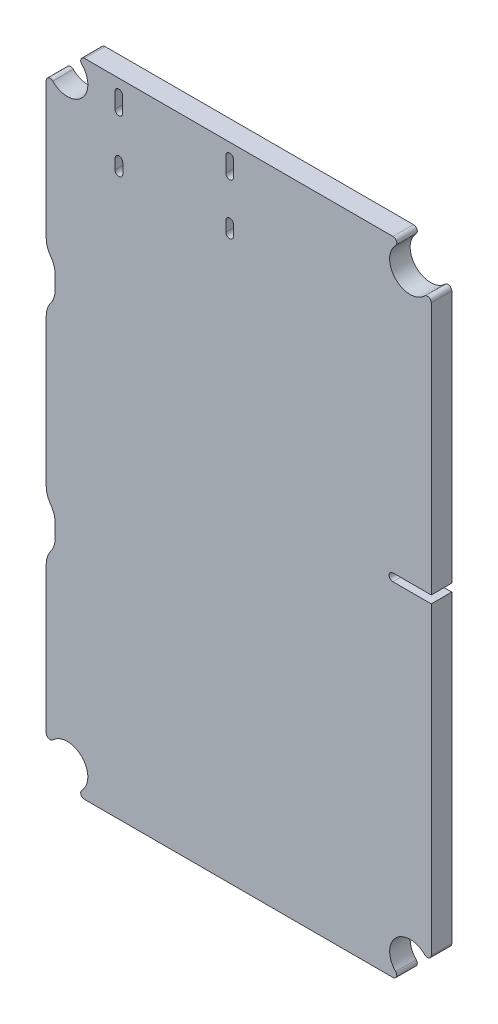
SolidWorks part; units mm, degrees
ref_plane "Front Plane" through (0, 0, 0) normal (0, 0, 1) x (1, 0, 0)
ref_plane "Top Plane" through (0, 0, 0) normal (0, 1, 0) x (1, 0, 0)
ref_plane "Right Plane" through (0, 0, 0) normal (1, 0, 0) x (0, 0, -1)
sketch "Sketch1" plane through (0, 0, 0) normal (0, 0, 1) x (1, 0, 0)
  line L40 (10, 12.987) -> (10, 24.35)
  line L41 (10.7, 26.5) -> (10.7, 27.5)
  line L42 (10, 29.65) -> (10, 41.1)
  line L43 (10.7, 43.25) -> (10.7, 44.25)
  line L44 (10, 46.4) -> (10, 57.013)
  line L45 (12.987, 60) -> (37.013, 60)
  line L46 (40, 57.013) -> (40, 12.987)
  line L47 (37.013, 10) -> (12.987, 10)
  arc A92 (10, 24.35) -> (10.35, 25.425) centre (11.8259, 24.35) cw
  arc A93 (10.35, 25.425) -> (10.7, 26.5) centre (8.8741, 26.5) ccw
  arc A94 (10.7, 27.5) -> (10.35, 28.575) centre (8.8741, 27.5) ccw
  arc A95 (10.35, 28.575) -> (10, 29.65) centre (11.8259, 29.65) cw
  arc A96 (10, 41.1) -> (10.35, 42.175) centre (11.8259, 41.1) cw
  arc A97 (10.35, 42.175) -> (10.7, 43.25) centre (8.8741, 43.25) ccw
  arc A98 (10.7, 44.25) -> (10.35, 45.325) centre (8.8741, 44.25) ccw
  arc A99 (10.35, 45.325) -> (10, 46.4) centre (11.8259, 46.4) cw
  arc A100 (10, 57.013) -> (10.5121, 57.2251) centre (10.3, 57.013) cw
  arc A101 (10.5121, 57.2251) -> (12.7749, 59.4879) centre (11.6449, 58.3551) ccw
  arc A102 (12.7749, 59.4879) -> (12.987, 60) centre (12.987, 59.7) cw
  arc A103 (37.013, 60) -> (37.2251, 59.4879) centre (37.013, 59.7) cw
  arc A104 (37.2251, 59.4879) -> (39.4879, 57.2251) centre (38.3551, 58.3551) ccw
  arc A105 (39.4879, 57.2251) -> (40, 57.013) centre (39.7, 57.013) cw
  arc A106 (40, 12.987) -> (39.4879, 12.7749) centre (39.7, 12.987) cw
  arc A107 (39.4879, 12.7749) -> (37.2251, 10.5121) centre (38.3579, 11.6421) ccw
  arc A108 (37.2251, 10.5121) -> (37.013, 10) centre (37.013, 10.3) cw
  arc A109 (12.987, 10) -> (12.7749, 10.5121) centre (12.987, 10.3) cw
  arc A110 (12.7749, 10.5121) -> (10.5121, 12.7749) centre (11.6421, 11.6421) ccw
  arc A111 (10.5121, 12.7749) -> (10, 12.987) centre (10.3, 12.987) cw
extrude "Board" add sketch "Sketch1" along normal blind 1.5994
sketch "Sketch17" plane through (0, 0, 1.5994) normal (0, 0, 1) x (1, 0, 0)
  line L0 (24.292, 58.964) -> (24.292, 57.764) construction
  line L1 (24.592, 58.964) -> (24.592, 57.764)
  line L2 (23.992, 58.964) -> (23.992, 57.764)
  line L3 (24.292, 54.584) -> (24.292, 53.784) construction
  line L4 (24.592, 54.584) -> (24.592, 53.784)
  line L5 (23.992, 54.584) -> (23.992, 53.784)
  line L6 (15.6645, 54.4652) -> (15.6645, 53.6652) construction
  line L7 (15.9645, 54.4652) -> (15.9645, 53.6652)
  line L8 (15.3645, 54.4652) -> (15.3645, 53.6652)
  line L9 (15.656, 58.964) -> (15.656, 57.764) construction
  line L10 (15.956, 58.964) -> (15.956, 57.764)
  line L11 (15.356, 58.964) -> (15.356, 57.764)
  arc A0 (24.592, 58.964) -> (23.992, 58.964) centre (24.292, 58.964) ccw
  arc A1 (23.992, 57.764) -> (24.592, 57.764) centre (24.292, 57.764) ccw
  arc A2 (24.592, 54.584) -> (23.992, 54.584) centre (24.292, 54.584) ccw
  arc A3 (23.992, 53.784) -> (24.592, 53.784) centre (24.292, 53.784) ccw
  arc A4 (15.9645, 54.4652) -> (15.3645, 54.4652) centre (15.6645, 54.4652) ccw
  arc A5 (15.3645, 53.6652) -> (15.9645, 53.6652) centre (15.6645, 53.6652) ccw
  arc A6 (15.956, 58.964) -> (15.356, 58.964) centre (15.656, 58.964) ccw
  arc A7 (15.356, 57.764) -> (15.956, 57.764) centre (15.656, 57.764) ccw
  point P2 (24.292, 58.364)
  point P8 (24.292, 54.184)
  point P15 (15.6645, 54.0652)
  point P22 (15.656, 58.364)
extrude "Cut-Extrude2" cut sketch "Sketch17" against normal through all
sketch "Sketch18" plane through (0, 0, 1.5994) normal (0, 0, 1) x (1, 0, 0)
  line L0 (37.015, 37.3) -> (41.715, 37.3)
  line L1 (41.715, 37.3) -> (41.715, 36.7)
  line L2 (41.715, 36.7) -> (37.015, 36.7)
  arc A0 (37.015, 36.7) -> (37.015, 37.3) centre (37.015, 37) cw
extrude "Cut-Extrude3" cut sketch "Sketch18" against normal through all
